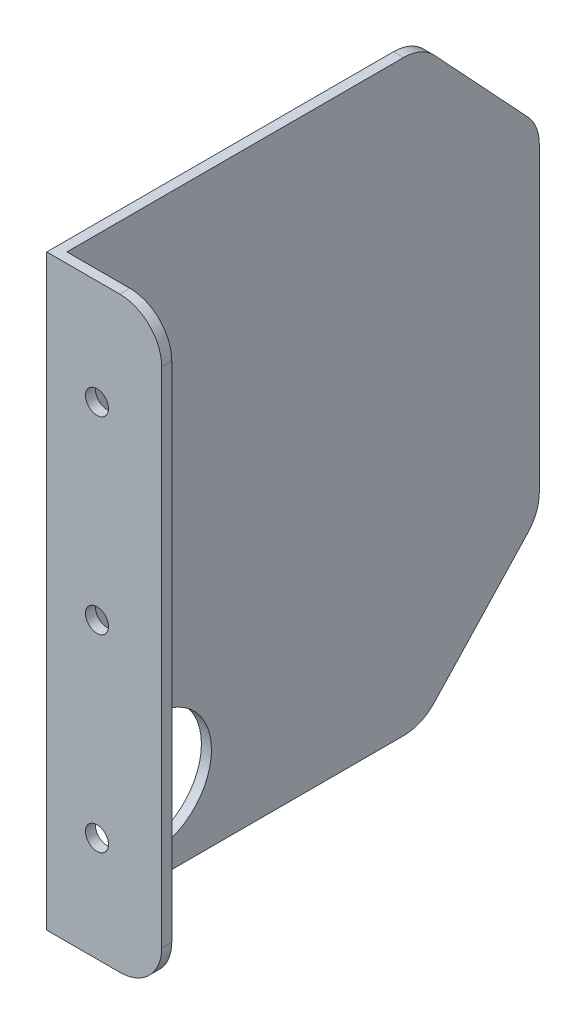
SolidWorks part; units mm, degrees
ref_plane "Front Plane" through (0, 0, 0) normal (0, 0, 1) x (1, 0, 0)
ref_plane "Top Plane" through (0, 0, 0) normal (0, 1, 0) x (1, 0, 0)
ref_plane "Right Plane" through (0, 0, 0) normal (1, 0, 0) x (0, 0, -1)
sketch "Sketch1" plane through (0, 0, 0) normal (1, 0, 0) x (0, 0, -1)
  line L1 (0, 0) -> (115, 0)
  line L2 (0, 0) -> (0, -140)
  line L3 (0, -140) -> (115, -140)
  line L4 (115, 0) -> (115, -140)
  dimension "D1" = 115
  dimension "D2" = 140
extrude "Boss-Extrude1" add sketch "Sketch1" along normal blind 2.4
sketch "Sketch2" plane through (2.4, 0, 0) normal (1, 0, 0) x (0, 0, -1)
  line L0 (87, 0) -> (115, -30)
  line L1 (115, 0) -> (0, 0) construction
  line L2 (115, -140) -> (115, 0) construction
  line L3 (115, -30) -> (142.6162, -32.5054)
  line L4 (142.6162, -32.5054) -> (142.6162, 14.8756)
  line L5 (142.6162, 14.8756) -> (87, 0)
  line L6 (115, -110) -> (87, -140)
  line L7 (0, -140) -> (115, -140) construction
  line L8 (87, -140) -> (87, -152.6611)
  line L9 (87, -152.6611) -> (136.31, -152.6611)
  line L10 (136.31, -152.6611) -> (115, -110)
  line L12 (0, 0) -> (0, -140) construction
  dimension "D1" = 30
  dimension "D2" = 87
  dimension "D3" = 87
  dimension "D4" = 30
extrude "Cut-Extrude1" cut sketch "Sketch2" against normal through all
fillet "Fillet1" radius 10 4 edges at (1.2, -140, -87) (1.2, -110, -115) (1.2, -30, -115) (1.2, 0, -87)
sketch "Sketch3" plane through (2.4, 0, 0) normal (1, 0, 0) x (0, 0, -1)
  line L0 (82.6545, 0) -> (0, 0) construction
  line L1 (0, -140) -> (2.4, -140)
  line L2 (0, -140) -> (0, 0)
  line L3 (0, 0) -> (2.4, 0)
  line L4 (2.4, -140) -> (2.4, 0)
  dimension "D1" = 2.4
extrude "Boss-Extrude2" add sketch "Sketch3" along normal blind 25
fillet "Fillet2" radius 10 2 edges at (27.4, -140, -1.2) (27.4, 0, -1.2)
sketch "Sketch4" plane through (0, 0, 0) normal (0, 0, 1) x (1, 0, 0)
  line L0 (17.4, 0) -> (0, 0) construction
  line L1 (17.4, -140) -> (0, -140) construction
  line L2 (27.4, -10) -> (27.4, -130) construction
  circle A0 centre (11.975, -70) radius 2.75
  circle A1 centre (11.975, -25) radius 2.75
  circle A2 centre (11.975, -115) radius 2.75
  point P12 (27.4, -70)
  dimension "D1" = 5.5
  dimension "D2" = 5.5
  dimension "D3" = 5.5
  dimension "D4" = 25
  dimension "D5" = 25
extrude "Cut-Extrude2" cut sketch "Sketch4" against normal through all
sketch "Sketch5" plane through (2.4, 0, 0) normal (1, 0, 0) x (0, 0, -1)
  line L1 (2.4, -140) -> (82.6545, -140) construction
  circle A0 centre (22.5917, -120) radius 14.275
  dimension "D2" = 28.55
  dimension "D1" = 20
extrude "Cut-Extrude3" cut sketch "Sketch5" against normal through all
